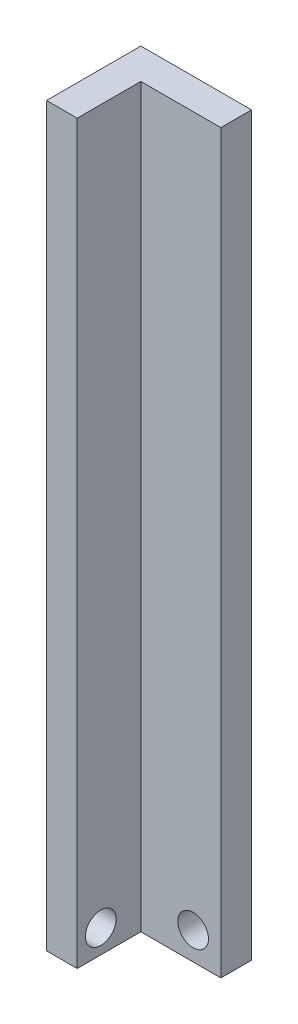
SolidWorks part; units mm, degrees
material "Stainless Steel (ferritic)"
ref_plane "Front Plane" through (0, 0, 0) normal (0, 0, 1) x (1, 0, 0)
ref_plane "Top Plane" through (0, 0, 0) normal (0, 1, 0) x (1, 0, 0)
ref_plane "Right Plane" through (0, 0, 0) normal (1, 0, 0) x (0, 0, -1)
sketch "Sketch1" plane through (0, 0, 0) normal (0, 1, 0) x (1, 0, 0)
  line L0 (30.3425, 60.6332) -> (30.3425, 66.1501) construction
  line L1 (-46.893, -60.7369) -> (46.893, -60.7369) construction
  line L2 (-46.893, -60.7369) -> (-46.893, 60.6332) construction
  line L3 (-46.893, 60.6332) -> (46.893, 60.6332) construction
  line L4 (46.893, -60.7369) -> (46.893, 60.6332) construction
  line L5 (-46.893, -60.7369) -> (46.893, 60.6332) construction
  line L6 (-46.893, 60.6332) -> (46.893, -60.7369) construction
  line L7 (30.3425, 44.0828) -> (63.4435, 44.0828) construction
  line L8 (30.3425, 44.0828) -> (30.3425, 77.1837) construction
  line L9 (30.3425, 77.1837) -> (63.4435, 77.1837) construction
  line L10 (63.4435, 44.0828) -> (63.4435, 77.1837) construction
  line L11 (30.3425, 44.0828) -> (63.4435, 77.1837) construction
  line L12 (30.3425, 77.1837) -> (63.4435, 44.0828) construction
  line L13 (30.3425, 66.1501) -> (52.4098, 66.1501) construction
  line L14 (52.4098, 66.1501) -> (52.4098, 44.0828) construction
  line L15 (52.4098, 44.0828) -> (46.893, 44.0828) construction
  line L16 (0, 60.6332) -> (0, -60.7369) construction
  line L17 (-46.893, -0.0518) -> (46.893, -0.0518) construction
  line L18 (-52.4098, 44.0828) -> (-46.893, 44.0828) construction
  line L19 (-52.4098, 66.1501) -> (-52.4098, 44.0828) construction
  line L20 (-30.3425, 66.1501) -> (-52.4098, 66.1501) construction
  line L21 (-30.3425, 60.6332) -> (-30.3425, 66.1501) construction
  line L22 (52.4098, -44.1864) -> (46.893, -44.1864) construction
  line L23 (52.4098, -66.2537) -> (52.4098, -44.1864) construction
  line L24 (30.3425, -66.2537) -> (52.4098, -66.2537) construction
  line L25 (30.3425, -60.7369) -> (30.3425, -66.2537) construction
  line L26 (-30.3425, -60.7369) -> (-30.3425, -66.2537) construction
  line L27 (-30.3425, -66.2537) -> (-52.4098, -66.2537) construction
  line L28 (-52.4098, -66.2537) -> (-52.4098, -44.1864) construction
  line L29 (-52.4098, -44.1864) -> (-46.893, -44.1864) construction
  line L30 (-63.4435, -81.9014) -> (-63.4435, 70.416)
  line L31 (-63.4435, 70.416) -> (63.4435, 70.416)
  line L32 (63.4435, -81.9014) -> (63.4435, 70.416) construction
  line L33 (-63.4435, -81.9014) -> (63.4435, -81.9014) construction
  line L34 (-30.3425, 83.116) -> (-76.1435, 83.116)
  line L35 (-76.1435, 83.116) -> (-76.1435, 44.0828)
  line L36 (-76.1435, 44.0828) -> (-63.4435, 44.0828)
  line L37 (-30.3425, 83.116) -> (-30.3425, 70.416)
  line L38 (-63.4435, 44.0828) -> (-63.4435, 70.416)
  point P0 (0, -0.0518)
  dimension "D1" = 12.7
  dimension "D2" = 12.7
extrude "Boss-Extrude1" add sketch "Sketch1" along normal blind 304.8 contours L37 L34 L35 L36 L30 L31
sketch "Sketch2" plane through (0, 0, -83.116) normal (0, 0, -1) x (-1, 0, 0)
  line L0 (30.3425, 0) -> (76.1435, 0) construction
  line L1 (76.1435, 304.8) -> (76.1435, 0) construction
  line L2 (30.3425, 0) -> (76.1435, 0)
  line L3 (76.1435, 304.8) -> (76.1435, 0)
  line L4 (53.243, 0) -> (53.243, 304.8) construction
  line L5 (30.3425, 304.8) -> (76.1435, 304.8) construction
  line L6 (30.3425, 11.4502) -> (53.243, 11.4502)
  line L7 (30.3425, 0) -> (53.243, 0)
  line L8 (30.3425, 0) -> (30.3425, 22.9005)
  line L9 (30.3425, 22.9005) -> (53.243, 22.9005)
  line L10 (53.243, 0) -> (53.243, 22.9005)
  line L11 (76.1435, 0) -> (53.243, 0)
  line L12 (76.1435, 0) -> (76.1435, 22.9005)
  line L14 (53.243, 0) -> (53.243, 22.9005)
  line L16 (41.7928, 22.9005) -> (41.7928, 0) construction
  circle A0 centre (41.7928, 11.4502) radius 6.35
  dimension "D1" = 12.7
extrude "Cut-Extrude1" cut sketch "Sketch2" against normal up to surface (12.7 mm away) contours L6 A0 | L6 A0 up to face at (-46.893, 152.4, -70.416)
sketch "Sketch3" plane through (-76.1435, 0, 0) normal (-1, 0, 0) x (0, 0, 1)
  line L0 (-83.116, 304.8) -> (-83.116, 0) construction
  line L1 (-83.116, 0) -> (-44.0828, 0) construction
  line L2 (-44.0828, 304.8) -> (-44.0828, 0) construction
  line L3 (-83.116, 304.8) -> (-83.116, 0) construction
  line L4 (-83.116, 0) -> (-44.0828, 0) construction
  line L5 (-44.0828, 304.8) -> (-44.0828, 0) construction
  line L6 (-63.5994, 0) -> (-63.5994, 304.8) construction
  line L7 (-83.116, 304.8) -> (-44.0828, 304.8) construction
  line L8 (-53.8411, 19.5166) -> (-53.8411, 0) construction
  line L9 (-44.0828, 0) -> (-63.5994, 0)
  line L10 (-44.0828, 0) -> (-44.0828, 19.5166)
  line L11 (-44.0828, 19.5166) -> (-63.5994, 19.5166) construction
  line L12 (-63.5994, 0) -> (-63.5994, 19.5166) construction
  circle A0 centre (-53.8411, 9.7583) radius 6.35
  dimension "D1" = 12.7
extrude "Cut-Extrude2" cut sketch "Sketch3" against normal up to surface (12.7 mm away) contours A0 up to face at (-63.4435, 152.4, -57.2494)
